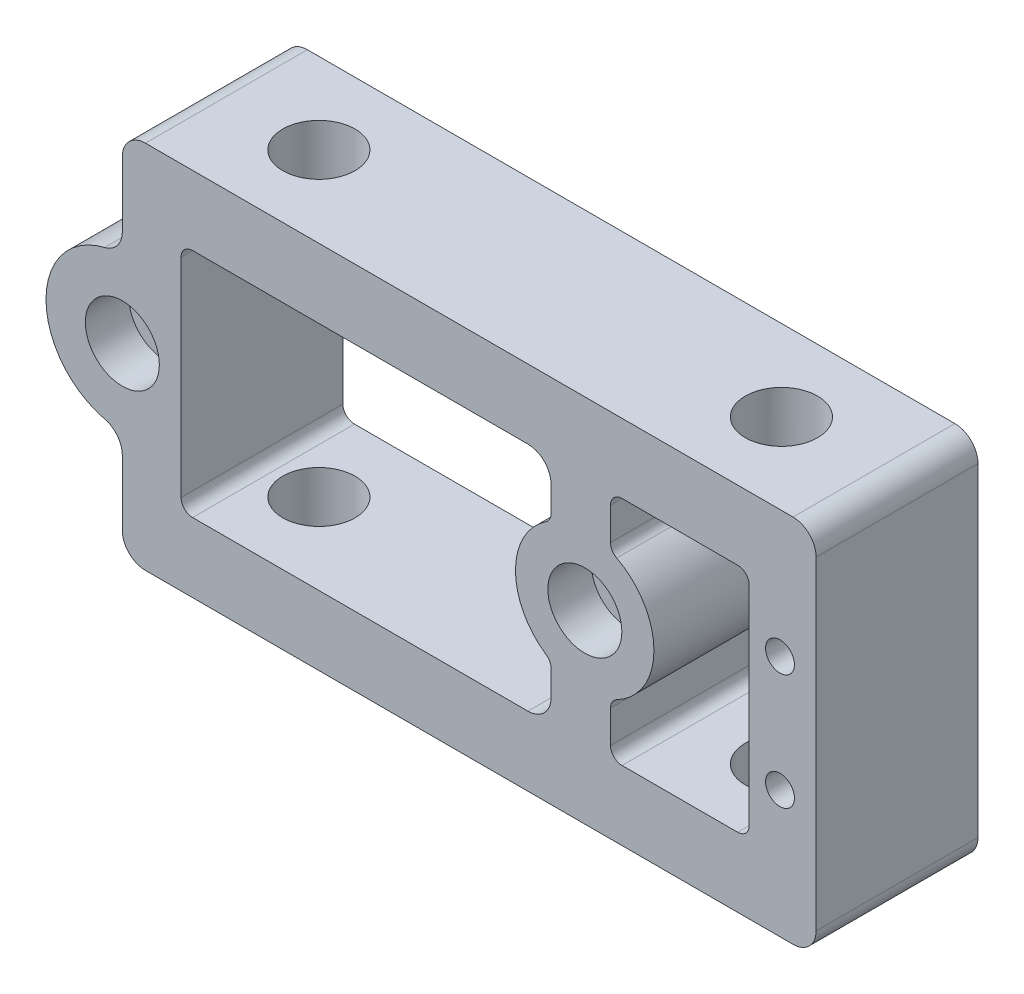
SolidWorks part; units mm, degrees
material "7075-T6, Plate (SS)"
ref_plane "X-Y Datum" through (0, 0, 0) normal (0, 0, 1) x (1, 0, 0)
ref_plane "X-Z Datum" through (0, 0, 0) normal (0, 1, 0) x (1, 0, 0)
ref_plane "Y-Z Datum" through (0, 0, 0) normal (1, 0, 0) x (0, 0, -1)
other "Graphic1"
other "Graphic (Closed) -1"
other "Graphic2"
other "Graphic (Closed) -2"
other "Graphic3"
other "Graphic (Closed) -3"
sketch "Sketch1" plane through (0, 0, 0) normal (0, 0, 1) x (1, 0, 0)
  line L5 (-93.6625, 0) -> (0, 0) construction
  line L7 (-93.6625, -20.32) -> (-93.6625, 20.32)
  line L17 (-93.6625, -20.32) -> (0, -20.32)
  line L28 (-12.7, 15.2978) -> (-12.7, -16.3411) construction
  line L30 (-93.6625, 20.32) -> (0, 20.32)
  line L31 (0, 20.32) -> (0, -20.32)
  circle A4 centre (-84.9313, 0) radius 2.4892
  circle A7 centre (-34.1313, 0) radius 2.4892
  circle A8 centre (-12.7, 6.35) radius 1.5875
  circle A9 centre (-12.7, -6.35) radius 1.5875
  point P1 (-93.6625, 0)
  dimension "D2" = 93.6625
  dimension "D3" = 34.1313
  dimension "D5" = 3.175
  dimension "D1" = 8.7312
  dimension "D4" = 40.64
  dimension "D6" = 6.35
  dimension "D7" = 6.35
  dimension "D8" = 12.7
extrude "Boss-Extrude1" add sketch "Sketch1" against normal blind 17.78
sketch "Sketch3" plane through (0, 0, 0) normal (0, 0, 1) x (1, 0, 0)
  circle A2 centre (-84.9313, 0) radius 4.064
  circle A3 centre (-84.9313, 0) radius 2.4892 construction
  circle A4 centre (-34.1313, 0) radius 4.064
  dimension "D1" = 8.128
sketch "Sketch6" plane through (0, 20.32, 0) normal (0, 1, 0) x (1, 0, 0)
  line L0 (0, 17.78) -> (-93.6625, 17.78) construction
  line L1 (-72.2313, 8.89) -> (-21.4312, 8.89) construction
  circle A0 centre (-72.2313, 8.89) radius 3.9687
  circle A1 centre (-21.4312, 8.89) radius 3.9687
  point P4 (-46.8312, 17.78)
  point P5 (-46.8312, 8.89)
  dimension "D1" = 7.9375
  dimension "D2" = 8.89
  dimension "D3" = 50.8
extrude "Cut-Extrude4" cut sketch "Sketch6" against normal through all
sketch "Sketch5" plane through (0, 0, 0) normal (0, 0, 1) x (1, 0, 0)
  line L7 (-46.8312, 20.32) -> (-46.8313, -20.32) construction
  line L8 (0, 20.32) -> (-93.6625, 20.32) construction
  line L18 (-93.6625, -20.32) -> (0, -20.32) construction
  line B0 (-93.6625, -20.32) -> (-93.6625, 20.32)
  line B1 (-84.9312, -20.32) -> (-93.6625, -20.32)
  line B2 (-84.9313, -10.6225) -> (-84.9312, -20.32)
  line B3 (-84.9313, 10.6225) -> (-84.9312, 20.32)
  line B4 (-93.6625, 20.32) -> (-84.9312, 20.32)
  arc B5 (-84.9313, -10.6225) -> (-86.8806, -8.1522) centre (-87.4713, -10.6225) ccw
  arc B6 (-86.8806, 8.1522) -> (-86.8806, -8.1522) centre (-84.9313, 0) ccw
  arc B7 (-84.9313, 10.6225) -> (-86.8806, 8.1522) centre (-87.4713, 10.6225) cw
  line B8 (0, -20.32) -> (0, 20.32)
  line B9 (-8.7313, -20.32) -> (0, -20.32)
  line B10 (-8.7313, -10.6225) -> (-8.7313, -20.32)
  line B11 (-8.7312, 10.6225) -> (-8.7312, 20.32)
  line B12 (0, 20.32) -> (-8.7312, 20.32)
  arc B13 (-8.7313, -10.6225) -> (-6.7819, -8.1522) centre (-6.1912, -10.6225) cw
  arc B14 (-6.7819, 8.1522) -> (-6.7819, -8.1522) centre (-8.7312, 0) cw
  arc B15 (-8.7312, 10.6225) -> (-6.7819, 8.1522) centre (-6.1912, 10.6225) ccw
sketch_block_instance "Block1-1"
sketch_block "Block1"
sketch_block_instance "Block1-2"
extrude "Cut-Extrude3" cut sketch "Sketch5" against normal up to surface (17.78 mm away) up to face at (-11.1125, -6.35, -17.78)
fillet "Fillet1" radius 2.54 4 edges at (-84.9312, -20.32, -8.89) (-8.7313, -20.32, -8.89) (-8.7312, 20.32, -8.89) (-84.9312, 20.32, -8.89)
extrude "Cut-Extrude5" cut sketch "Sketch3" against normal blind 4.7752
ref_point "Point1"
ref_point "Point2"
sketch "Sketch7" plane through (0, 0, 0) normal (0, 0, 1) x (1, 0, 0)
  line L0 (-46.8312, 20.32) -> (-46.8313, -20.32) construction
  line L5 (-11.2713, 20.32) -> (-82.3912, 20.32) construction
  line L6 (-82.3912, -20.32) -> (-11.2713, -20.32) construction
  line L7 (-37.8425, 10.16) -> (-37.8425, 6.6551)
  line L8 (-60.7025, -12.7) -> (-40.3825, -12.7)
  line L9 (-63.2425, -10.16) -> (-63.2425, 10.16)
  line L10 (-60.7025, 12.7) -> (-40.3825, 12.7)
  line L14 (-37.8425, -10.16) -> (-37.8425, -6.6551)
  line L17 (-8.7313, -10.6225) -> (-8.7313, -17.78) construction
  line L18 (-8.7312, 10.6225) -> (-8.7313, -10.6225)
  line L19 (-8.7313, -10.6225) -> (0.3823, -10.6225)
  line L20 (0.3823, -10.6225) -> (0.3823, 10.6225)
  line L21 (0.3823, 10.6225) -> (-8.7312, 10.6225)
  arc A0 (-60.7025, -12.7) -> (-63.2425, -10.16) centre (-60.7025, -10.16) cw
  arc A1 (-40.3825, -12.7) -> (-37.8425, -10.16) centre (-40.3825, -10.16) ccw
  arc A2 (-40.3825, 12.7) -> (-37.8425, 10.16) centre (-40.3825, 10.16) cw
  arc A3 (-63.2425, 10.16) -> (-60.7025, 12.7) centre (-60.7025, 10.16) cw
  arc A5 (-37.8425, -6.6551) -> (-37.8425, 6.6551) centre (-34.1313, 0) cw
  point P0 (-46.8313, 0)
  point P1 (-41.7513, 0)
  point P26 (-63.2425, 0)
  dimension "D3" = 2.54
  dimension "D4" = 7.62
  dimension "D1" = 25.4
  dimension "D2" = 25.4
extrude "Cut-Extrude6" cut sketch "Sketch7" against normal through all
sketch "Sketch8" plane through (0, 0, 0) normal (0, 0, 1) x (1, 0, 0)
  line L2 (-78.4825, -12.7) -> (-78.4825, 12.7)
  line L5 (-82.3912, -20.32) -> (-11.2713, -20.32) construction
  line L9 (-31.3164, 12.7) -> (-16.0764, 12.7)
  line L10 (-16.0764, 12.7) -> (-16.0764, -12.7)
  line L11 (-16.0764, -12.7) -> (-31.3164, -12.7)
  line L15 (-31.3164, 7.0466) -> (-31.3164, 12.7)
  line L16 (-31.3164, -7.0466) -> (-31.3164, -12.7)
  line L17 (-8.7312, 17.78) -> (-8.7313, -17.78) construction
  line L18 (-78.4825, 12.7) -> (-60.7025, 12.7)
  line L19 (-60.7025, 12.7) -> (-60.7025, -12.7)
  line L20 (-60.7025, -12.7) -> (-78.4825, -12.7)
  arc A0 (-31.3164, 7.0466) -> (-31.3164, -7.0466) centre (-34.1313, 0) cw
  point P4 (-78.4825, 0)
  point P16 (-16.0764, 0)
  point P19 (-26.5433, 0)
  dimension "D4" = 7.588
  dimension "D1" = 17.78
  dimension "D2" = 20.32
  dimension "D5" = 15.24
  dimension "D6" = 25.4
  dimension "D7" = 20.32
  dimension "D8" = 7.3452
extrude "Cut-Extrude7" cut sketch "Sketch8" against normal up to surface (17.78 mm away) up to face at (-48.3934, 0, -17.78)
fillet "Fillet2" radius 1.27 10 edges at (-31.3164, -12.7, -8.89) (-16.0764, -12.7, -8.89) (-16.0764, 12.7, -8.89) (-31.3164, 12.7, -8.89) (-31.3164, 7.0466, -8.89) (-31.3164, -7.0466, -8.89) (-37.8425, -6.6551, -8.89) (-37.8425, 6.6551, -8.89) (-78.4825, -12.7, -8.89) (-78.4825, 12.7, -8.89)
